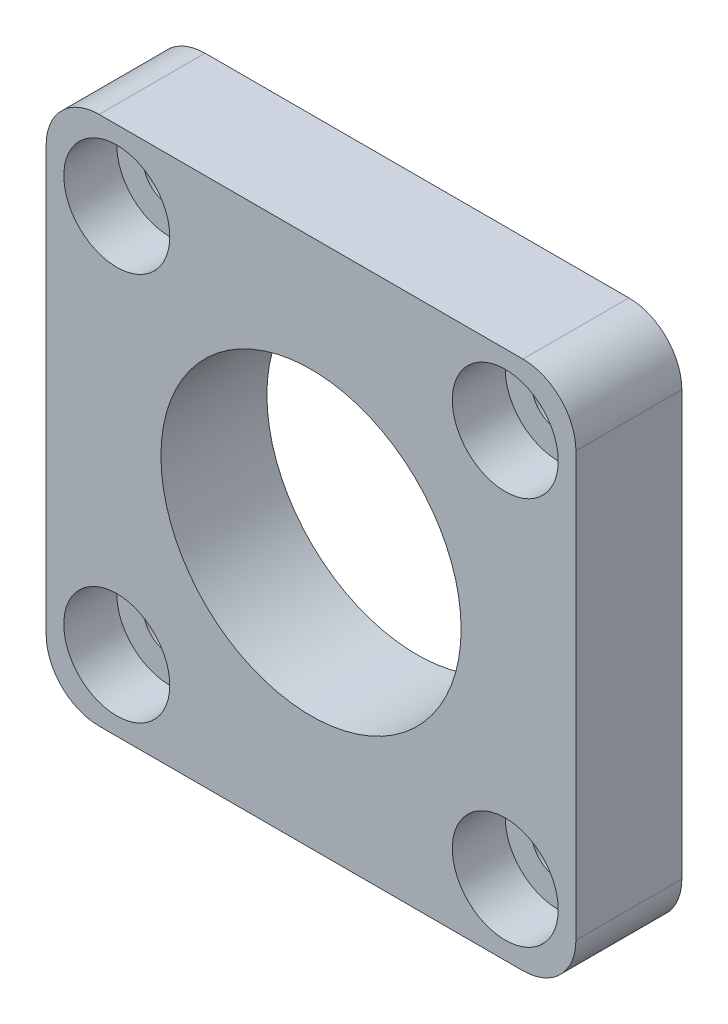
SolidWorks part; units mm, degrees
ref_plane "Front Plane" through (0, 0, 0) normal (0, 0, 1) x (1, 0, 0)
ref_plane "Top Plane" through (0, 0, 0) normal (0, 1, 0) x (1, 0, 0)
ref_plane "Right Plane" through (0, 0, 0) normal (1, 0, 0) x (0, 0, -1)
sketch "Sketch1" plane through (0, 0, 0) normal (0, 0, 1) x (1, 0, 0)
  line L1 (-15, -15) -> (15, -15)
  line L2 (-15, -15) -> (-15, 15)
  line L3 (-15, 15) -> (15, 15)
  line L4 (15, -15) -> (15, 15)
  line L5 (-15, -15) -> (15, 15) construction
  line L6 (-15, 15) -> (15, -15) construction
  circle A0 centre (0, 0) radius 8.5
  point P0 (0, 0)
  dimension "D3" = 17
  dimension "D1" = 30
  dimension "D2" = 30
extrude "Boss-Extrude1" add sketch "Sketch1" along normal blind 6
sketch "Sketch3" plane through (0, 0, 6) normal (0, 0, 1) x (1, 0, 0)
  line L1 (-11, -11) -> (11, -11) construction
  line L2 (-11, -11) -> (-11, 11) construction
  line L3 (-11, 11) -> (11, 11) construction
  line L4 (11, -11) -> (11, 11) construction
  line L5 (-11, -11) -> (11, 11) construction
  line L6 (-11, 11) -> (11, -11) construction
  circle A0 centre (-11, 11) radius 1.5
  circle A1 centre (11, 11) radius 1.5
  circle A2 centre (11, -11) radius 1.5
  circle A3 centre (-11, -11) radius 1.5
  point P0 (0, 0)
  dimension "D3" = 3
  dimension "D4" = 3
  dimension "D5" = 3
  dimension "D6" = 3
  dimension "D1" = 22
  dimension "D2" = 22
extrude "Cut-Extrude2" cut sketch "Sketch3" against normal through all
sketch "Sketch4" plane through (0, 0, 6) normal (0, 0, 1) x (1, 0, 0)
  circle A0 centre (-11, 11) radius 3
  circle A1 centre (11, 11) radius 3
  circle A2 centre (11, -11) radius 3
  circle A3 centre (-11, -11) radius 3
  dimension "D1" = 6
  dimension "D2" = 6
  dimension "D3" = 6
  dimension "D4" = 6
extrude "Cut-Extrude3" cut sketch "Sketch4" against normal blind 3
fillet "Fillet1" radius 3 4 edges at (-15, -15, 3) (15, -15, 3) (15, 15, 3) (-15, 15, 3)
